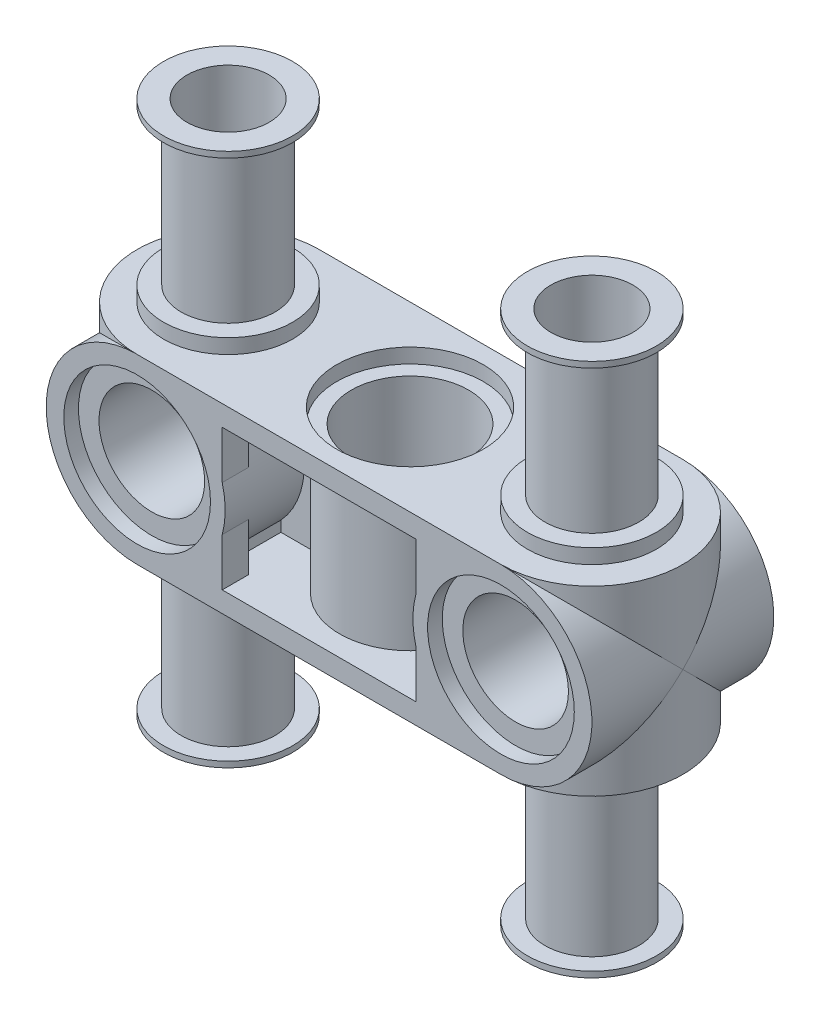
SolidWorks part; units mm, degrees
material "PVC Rigid"
ref_plane "Front Plane" through (0, 0, 0) normal (0, 0, 1) x (1, 0, 0)
ref_plane "Top Plane" through (0, 0, 0) normal (0, 1, 0) x (1, 0, 0)
ref_plane "Right Plane" through (0, 0, 0) normal (1, 0, 0) x (0, 0, -1)
sketch "Sketch1" plane through (0, 0, 0) normal (0, 1, 0) x (1, 0, 0)
  line L0 (-19.2625, 0) -> (26.4221, 0) construction
  line L1 (-7.874, 3.937) -> (7.874, 3.937)
  line L2 (0, 0) -> (0, 11.754) construction
  line L3 (7.874, -3.937) -> (-7.874, -3.937)
  circle A0 centre (-7.874, 0) radius 2.54 construction
  circle A1 centre (0, 0) radius 2.54 construction
  circle A2 centre (7.874, 0) radius 2.54 construction
  arc A3 (7.874, -3.937) -> (7.874, 3.937) centre (7.874, 0) ccw
  arc A4 (-7.874, 3.937) -> (-7.874, -3.937) centre (-7.874, 0) ccw
  dimension "D3" = 5.08
  dimension "D4" = 7.874
  dimension "D1" = 7.874
  dimension "D2" = 7.874
extrude "Extrude1" add sketch "Sketch1" along normal blind 3.937
sketch "Sketch2" plane through (0, 0, 0) normal (0, -1, 0) x (1, 0, 0)
  circle A0 centre (0, 0) radius 2.794
  dimension "D1" = 5.588
extrude "Cut-Extrude1" cut sketch "Sketch2" against normal blind 0.254
sketch "Sketch3" plane through (0, 0, 0) normal (0, -1, 0) x (1, 0, 0)
  circle A0 centre (7.874, 0) radius 2.794
  circle A1 centre (-7.874, 0) radius 2.794
  arc A2 (-7.874, 3.937) -> (-7.874, -3.937) centre (-7.874, 0) ccw construction
  arc A3 (7.874, -3.937) -> (7.874, 3.937) centre (7.874, 0) ccw construction
  dimension "D1" = 5.588
extrude "Extrude2" add sketch "Sketch3" along normal blind 0.635
sketch "Sketch5" plane through (0, -0.635, 0) normal (0, -1, 0) x (1, 0, 0)
  circle A0 centre (7.874, 0) radius 2.794 construction
  circle A1 centre (7.874, 0) radius 2.032
  circle A2 centre (-7.874, 0) radius 2.794 construction
  circle A3 centre (7.874, 0) radius 1.778
  circle A4 centre (-7.874, 0) radius 2.032
  circle A8 centre (-7.874, 0) radius 1.778
  dimension "D2" = 4.064
  dimension "D1" = 3.556
extrude "Extrude4" add sketch "Sketch5" along normal blind 6.985
sketch "Sketch6" plane through (0, -7.62, 0) normal (0, -1, 0) x (1, 0, 0)
  circle A1 centre (-7.874, 0) radius 1.778 construction
  circle A3 centre (7.874, 0) radius 1.778 construction
  circle A4 centre (-7.874, 0) radius 2.794 construction
  circle A5 centre (7.874, 0) radius 2.794 construction
  circle A6 centre (-7.874, 0) radius 2.794
  circle A7 centre (7.874, 0) radius 2.794
  circle A8 centre (7.874, 0) radius 1.778
  circle A9 centre (-7.874, 0) radius 1.778
extrude "Extrude5" add sketch "Sketch6" against normal blind 0.254
sketch "Sketch7" plane through (0, 0, -3.937) normal (0, 0, -1) x (-1, 0, 0)
  line L0 (-7.874, 3.937) -> (7.874, 3.937) construction
  line L2 (-7.874, 0) -> (7.874, 0) construction
  line L3 (-7.874, 0) -> (7.874, 0)
  line L4 (-7.874, 3.937) -> (7.874, 3.937)
  line L5 (-7.874, 3.937) -> (-11.811, 3.937)
  line L6 (7.874, 3.937) -> (11.811, 3.937)
  arc A0 (-11.811, 3.937) -> (-7.874, 0) centre (-7.874, 3.937) ccw
  arc A1 (7.874, 0) -> (11.811, 3.937) centre (7.874, 3.937) ccw
extrude "Extrude6" add sketch "Sketch7" against normal blind 7.874
sketch "Sketch8" plane through (0, 3.937, 0) normal (0, 1, 0) x (1, 0, 0)
  circle A0 centre (-7.874, 0) radius 2.54 construction
  circle A1 centre (0, 0) radius 2.54 construction
  circle A2 centre (7.874, 0) radius 2.54 construction
  circle A3 centre (-7.874, 0) radius 2.54 construction
  circle A4 centre (0, 0) radius 2.54
  circle A5 centre (7.874, 0) radius 2.54 construction
extrude "Cut-Extrude2" cut sketch "Sketch8" against normal blind 3.556
sketch "Sketch9" plane through (0, 0, 3.937) normal (0, 0, 1) x (1, 0, 0)
  circle A0 centre (7.874, 3.937) radius 2.286
  circle A1 centre (-7.874, 3.937) radius 2.286
  dimension "D1" = 4.572
extrude "Cut-Extrude3" cut sketch "Sketch9" against normal through all
sketch "Sketch10" plane through (0, 0, 3.937) normal (0, 0, 1) x (1, 0, 0)
  circle A0 centre (7.874, 3.937) radius 3.175
  circle A1 centre (-7.874, 3.937) radius 3.175
  dimension "D1" = 6.35
extrude "Cut-Extrude4" cut sketch "Sketch10" against normal blind 0.635
mirror "Mirror2" about plane through (0, 0, 0) normal (0, 0, 1) of "Cut-Extrude4"
sketch "Sketch11" plane through (0, 3.937, 0) normal (0, 1, 0) x (1, 0, 0)
  line L0 (-5.08, -0.508) -> (-5.08, -2.794)
  line L1 (5.08, 0.508) -> (5.08, 2.794)
  line L2 (5.08, -2.794) -> (5.08, -0.508)
  line L15 (-4.191, -3.429) -> (4.191, -3.429)
  line L23 (4.699, 3.937) -> (-4.699, 3.937) construction
  line L24 (-5.809, 0) -> (6.5071, 0) construction
  line L25 (-5.08, 0.508) -> (-3.0054, 0.508)
  line L26 (-5.809, 0.508) -> (6.5071, 0.508) construction
  line L27 (-5.08, -0.508) -> (-3.0054, -0.508)
  line L28 (-5.809, -0.508) -> (6.5071, -0.508) construction
  line L29 (-4.699, -3.937) -> (4.699, -3.937) construction
  line L30 (-4.191, -3.937) -> (4.191, -3.937)
  line L31 (3.0054, -0.508) -> (5.08, -0.508)
  line L32 (-4.191, -2.794) -> (-4.191, -3.429)
  line L34 (4.191, -3.429) -> (4.191, -2.794)
  line L35 (4.191, -2.794) -> (5.08, -2.794)
  line L36 (5.08, -2.794) -> (5.08, 2.794)
  line L37 (4.191, 3.429) -> (-4.191, 3.429)
  line L38 (4.191, 3.937) -> (-4.191, 3.937)
  line L39 (-4.191, 3.429) -> (-4.191, 2.794)
  line L40 (-5.08, 2.794) -> (-5.08, -2.794)
  line L41 (-5.08, -2.794) -> (-4.191, -2.794)
  line L42 (-4.191, -2.794) -> (-4.191, -3.937)
  line L43 (3.0054, 0.508) -> (5.08, 0.508)
  line L44 (4.191, -3.937) -> (4.191, -2.794)
  line L45 (4.191, -2.794) -> (5.08, -2.794)
  line L47 (-4.191, 3.937) -> (-4.191, 2.794)
  line L49 (-4.191, 2.794) -> (-5.08, 2.794)
  line L50 (-5.08, 2.794) -> (-5.08, 0.508)
  line L51 (-5.08, -2.794) -> (-4.191, -2.794)
  line L65 (-4.191, 2.794) -> (-5.08, 2.794)
  line L70 (5.08, 2.794) -> (4.191, 2.794)
  line L71 (5.08, 2.794) -> (4.191, 2.794)
  line L72 (4.191, 2.794) -> (4.191, 3.429)
  line L73 (4.191, 2.794) -> (4.191, 3.937)
  circle A5 centre (0, 0) radius 3.048
  arc A6 (-3.0054, -0.508) -> (3.0054, -0.508) centre (0, 0) ccw
  arc A8 (3.0054, 0.508) -> (-3.0054, 0.508) centre (0, 0) ccw
  dimension "D1" = 0.508
  dimension "D2" = 0.508
  dimension "D3" = 0.508
  dimension "D4" = 0.508
extrude "Cut-Extrude6" cut sketch "Sketch11" against normal blind 3.048
sketch "Sketch13" plane through (0, 0.381, 0) normal (0, 1, 0) x (1, 0, 0)
  circle A1 centre (0, 0) radius 2.54
  circle A2 centre (0, 0) radius 2.54
  dimension "D1" = 0
extrude "Cut-Extrude7" cut sketch "Sketch13" against normal through all
sketch "Sketch14" plane through (0, 0, 0) normal (0, -1, 0) x (1, 0, 0)
  circle A0 centre (0, 0) radius 3.175
  dimension "D1" = 6.35
extrude "Cut-Extrude8" cut sketch "Sketch14" against normal blind 0.635
sketch "Sketch17" plane through (0, 0, 3.937) normal (0, 0, 1) x (1, 0, 0)
  line L0 (-4.064, 3.937) -> (-4.699, 3.937)
  line L1 (-11.049, 3.937) -> (-11.684, 3.937)
  arc A0 (-11.684, 3.937) -> (-4.064, 3.937) centre (-7.874, 3.937) ccw
  arc A1 (-11.049, 3.937) -> (-4.699, 3.937) centre (-7.874, 3.937) ccw construction
  arc A2 (-11.049, 3.937) -> (-4.699, 3.937) centre (-7.874, 3.937) ccw
  dimension "D1" = 3.81
extrude "Extrude8" add sketch "Sketch17" against normal blind 7.112
mirror "Mirror3" about plane through (0, 0, 0) normal (1, 0, 0) of "Extrude8"
mirror "Mirror1"
